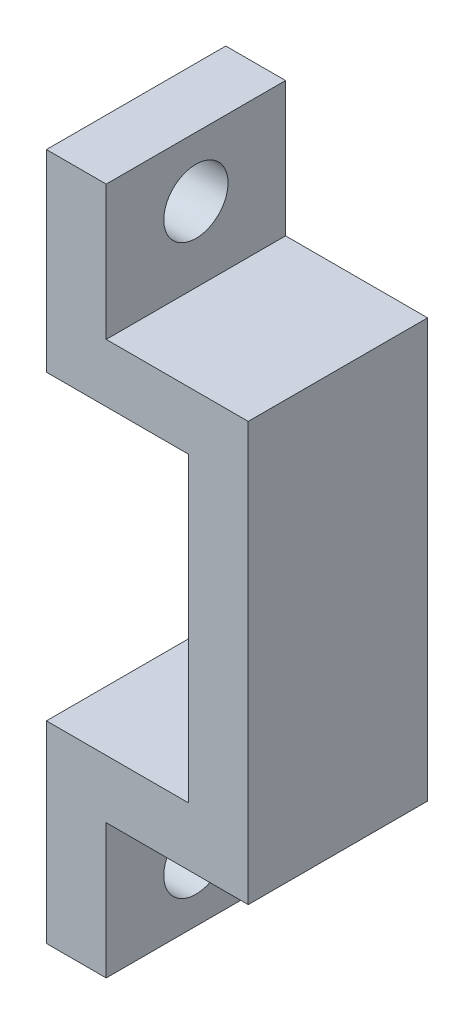
SolidWorks part; units mm, degrees
ref_plane "前视基准面" through (0, 0, 0) normal (0, 0, 1) x (1, 0, 0)
ref_plane "上视基准面" through (0, 0, 0) normal (0, 1, 0) x (1, 0, 0)
ref_plane "右视基准面" through (0, 0, 0) normal (1, 0, 0) x (0, 0, -1)
sketch "Sketch1" plane through (0, 0, 0) normal (0, 0, 1) x (1, 0, 0)
  line L0 (82.5, 84.6677) -> (82.5, 71.7677)
  line L1 (82.5, 71.7677) -> (92, 71.7677)
  line L2 (92, 71.7677) -> (92, 51.5677)
  line L3 (92, 51.5677) -> (82.5, 51.5677)
  line L4 (82.5, 51.5677) -> (82.5, 38.6677)
  line L5 (82.5, 38.6677) -> (86.5, 38.6677)
  line L6 (86.5, 38.6677) -> (86.5, 47.6677)
  line L7 (86.5, 47.6677) -> (96, 47.6677)
  line L8 (96, 47.6677) -> (96, 75.6677)
  line L9 (96, 75.6677) -> (86.5, 75.6677)
  line L10 (86.5, 75.6677) -> (86.5, 84.6677)
  line L11 (86.5, 84.6677) -> (82.5, 84.6677)
  line L13 (72, 71.7677) -> (82, 71.7677) construction
  line L14 (82, 51.5677) -> (72, 51.5677) construction
  line L15 (68, 47.6677) -> (78, 47.6677) construction
  line L16 (78, 75.6677) -> (66.9, 75.6677) construction
  line L17 (82, 71.7677) -> (82, 84.6677) construction
  line L18 (72, 71.7677) -> (72, 51.5677) construction
  line L19 (78, 38.6677) -> (82, 38.6677) construction
  line L20 (82, 84.6677) -> (78, 84.6677) construction
  dimension "D1" = 0.5
  dimension "D2" = 4
  dimension "D3" = 4
  dimension "D4" = 20
extrude "Boss-Extrude1" add sketch "Sketch1" against normal up to vertex (12 mm away)
sketch "Sketch2" plane through (86.5, 0, 0) normal (1, 0, 0) x (0, 0, -1)
  circle A0 centre (6, 42.6677) radius 2.15 construction
  circle A1 centre (6, 80.6677) radius 2.15 construction
  circle A2 centre (6, 42.6677) radius 2.15
  circle A3 centre (6, 80.6677) radius 2.15
extrude "Cut-Extrude1" cut sketch "Sketch2" against normal blind 39
